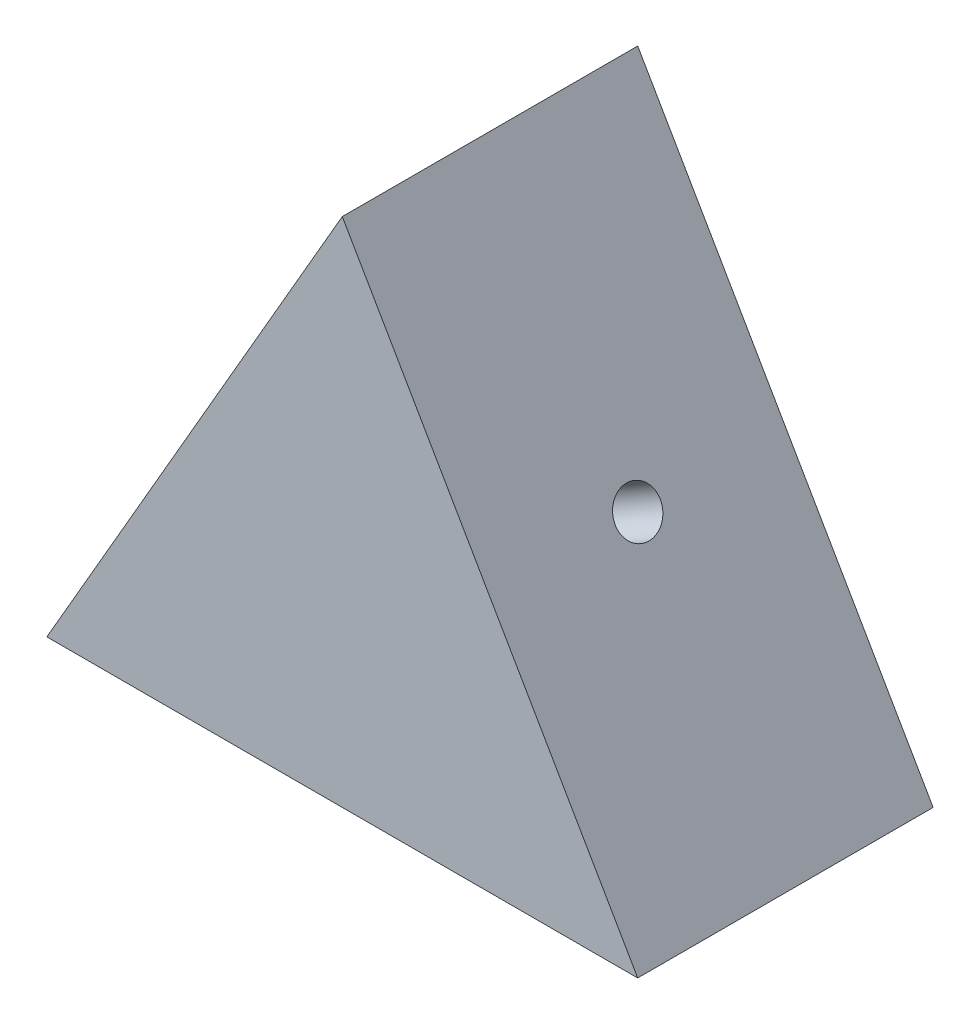
SolidWorks part; units mm, degrees
ref_plane "Front Plane" through (0, 0, 0) normal (0, 0, 1) x (1, 0, 0)
ref_plane "Top Plane" through (0, 0, 0) normal (0, 1, 0) x (1, 0, 0)
ref_plane "Right Plane" through (0, 0, 0) normal (1, 0, 0) x (0, 0, -1)
sketch "Sketch1" plane through (0, 0, 0) normal (0, 0, 1) x (1, 0, 0)
  line L0 (0, 0) -> (250, 0)
  line L2 (250, 0) -> (0, 433.0127)
  line L3 (0, 0) -> (-250, 0)
  line L4 (-250, 0) -> (0, 433.0127)
  dimension "D1" = 433.0127
  dimension "D2" = 250
  dimension "D3" = 250
extrude "Boss-Extrude1" add sketch "Sketch1" along normal blind 250 contours L0 L2 L4 L3
sketch "Sketch2" plane through (187.5, 108.2532, 0) normal (0.866, 0.5, 0) x (0, 0, -1)
  circle A0 centre (-125, 125) radius 19.05
  dimension "D1" = 38.1
extrude "Cut-Extrude1" cut sketch "Sketch2" against normal blind 76.2
sketch "Sketch3" plane through (0, 0, 0) normal (0, -1, 0) x (1, 0, 0)
  circle A0 centre (0, 125) radius 19.05
  dimension "D1" = 38.1
extrude "Cut-Extrude2" cut sketch "Sketch3" against normal blind 76.2
sketch "Sketch4" plane through (-187.5, 108.2532, 0) normal (-0.866, 0.5, 0) x (0, 0, 1)
  circle A0 centre (125, 125) radius 19.05
  dimension "D1" = 38.1
extrude "Cut-Extrude3" cut sketch "Sketch4" against normal blind 76.2
equation "\"0..25m\"=0.01"
equation "\"0..0762m\"=0.1016"
